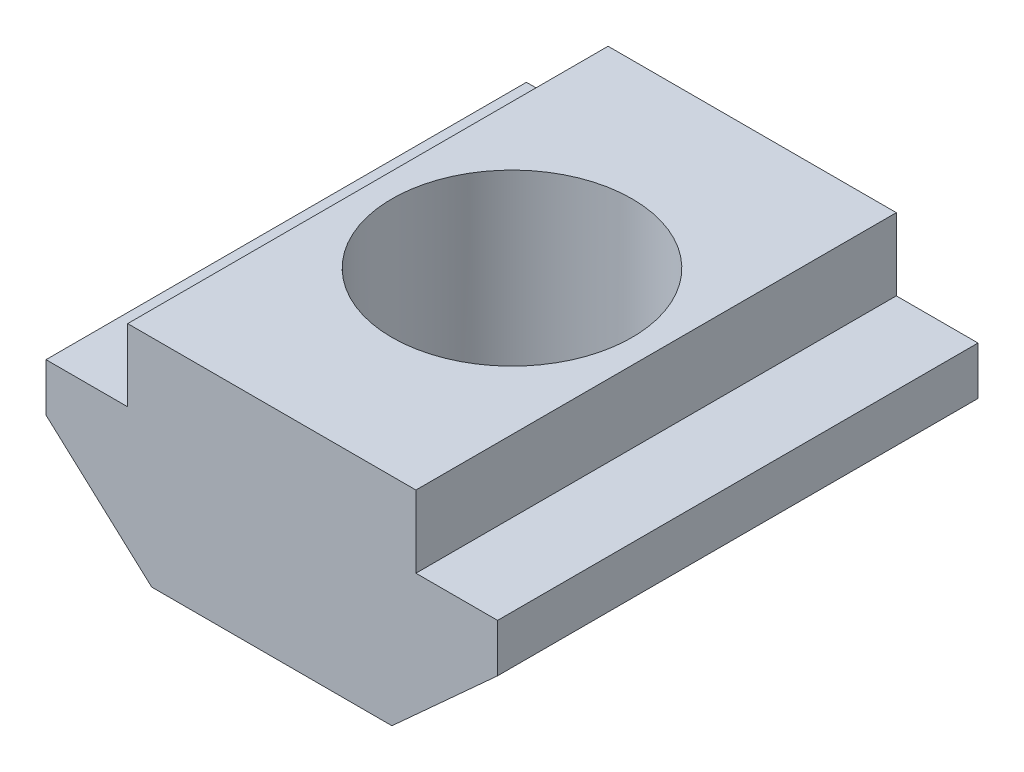
SolidWorks part; units mm, degrees
material "Сталь 10 ГОСТ 535-88"
ref_plane "Спереди" through (0, 0, 0) normal (0, 0, 1) x (1, 0, 0)
ref_plane "Сверху" through (0, 0, 0) normal (0, 1, 0) x (1, 0, 0)
ref_plane "Справа" through (0, 0, 0) normal (1, 0, 0) x (0, 0, -1)
sketch "Эскиз1" plane through (0, 0, 0) normal (0, 0, 1) x (1, 0, 0)
  line L0 (3, 0) -> (-3, 0)
  line L1 (-3, 0) -> (-3, -1.5)
  line L2 (-3, -1.5) -> (-4.7, -1.5)
  line L3 (-4.7, -1.5) -> (-4.7, -2.5)
  line L4 (-4.7, -2.5) -> (-2.5, -4.5)
  line L5 (-2.5, -4.5) -> (2.5, -4.5)
  line L6 (0, 0) -> (0, -5.8239) construction
  line L7 (4.7, -2.5) -> (2.5, -4.5)
  line L8 (4.7, -1.5) -> (4.7, -2.5)
  line L9 (3, -1.5) -> (4.7, -1.5)
  line L10 (3, 0) -> (3, -1.5)
  point P11 (0, -4.5)
  dimension "D1" = 3
  dimension "D2" = 1.5
  dimension "D3" = 3
  dimension "D4" = 4.7
  dimension "D5" = 1
  dimension "D6" = 2.5
extrude "Бобышка-Вытянуть1" add sketch "Эскиз1" along normal mid plane 10
sketch "Эскиз2" plane through (0, 0, 0) normal (0, 1, 0) x (1, 0, 0)
  circle A0 centre (0, 0) radius 2.5
  dimension "D1" = 5
extrude "Вырез-Вытянуть1" cut sketch "Эскиз2" against normal through all
